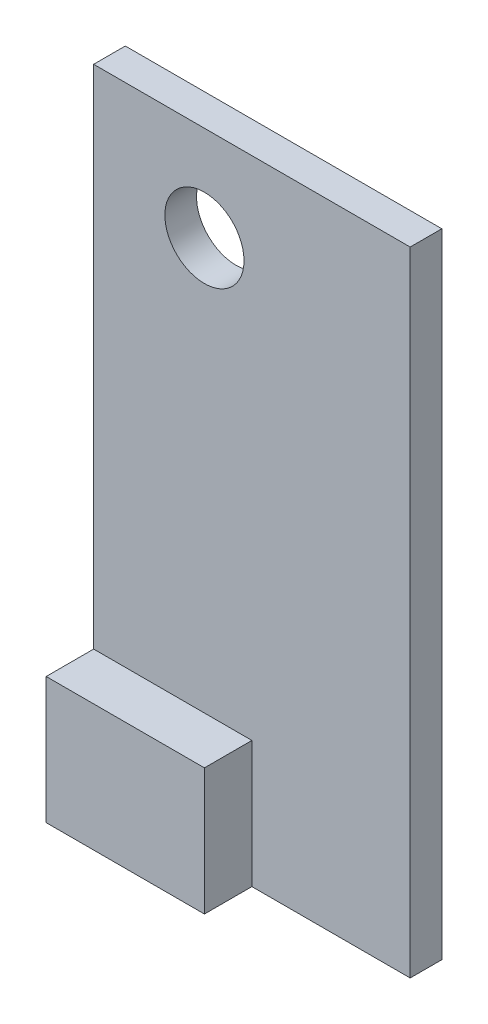
SolidWorks part; units mm, degrees
ref_plane "Front Plane" through (0, 0, 0) normal (0, 0, 1) x (1, 0, 0)
ref_plane "Top Plane" through (0, 0, 0) normal (0, 1, 0) x (1, 0, 0)
ref_plane "Right Plane" through (0, 0, 0) normal (1, 0, 0) x (0, 0, -1)
sketch "Sketch2" plane through (0, 0, 0) normal (0, 0, 1) x (1, 0, 0)
  line L0 (0, 0) -> (100, 0)
  line L1 (100, 0) -> (100, 200)
  line L2 (100, 200) -> (0, 200)
  line L3 (0, 200) -> (0, 0)
  dimension "D1" = 200
  dimension "D2" = 100
extrude "Boss-Extrude1" add sketch "Sketch2" along normal blind 10
sketch "Sketch3" plane through (0, 0, 0) normal (0, 0, 1) x (1, 0, 0)
  line L0 (0, 0) -> (50, 0)
  line L1 (0, 0) -> (100, 0) construction
  line L2 (50, 0) -> (50, 40)
  line L3 (50, 40) -> (0, 40)
  line L4 (0, 200) -> (0, 0) construction
  line L5 (0, 40) -> (0, 0)
  line L6 (0, 0) -> (50, 0)
  dimension "D1" = 50
  dimension "D2" = 40
extrude "Boss-Extrude3" add sketch "Sketch3" along normal blind 25 contours L5 L0 L2 L3
sketch "Sketch8" plane through (0, 0, 25) normal (0, 0, 1) x (1, 0, 0)
  line L0 (0, 200) -> (0, 40) construction
  line L1 (100, 200) -> (0, 200) construction
  circle A0 centre (35, 170) radius 12.5
  point P2 (0, 0)
  point P5 (0, 0)
  dimension "D3" = 25
  dimension "D1" = 35
  dimension "D2" = 30
extrude "Cut-Extrude2" cut sketch "Sketch8" against normal through all
